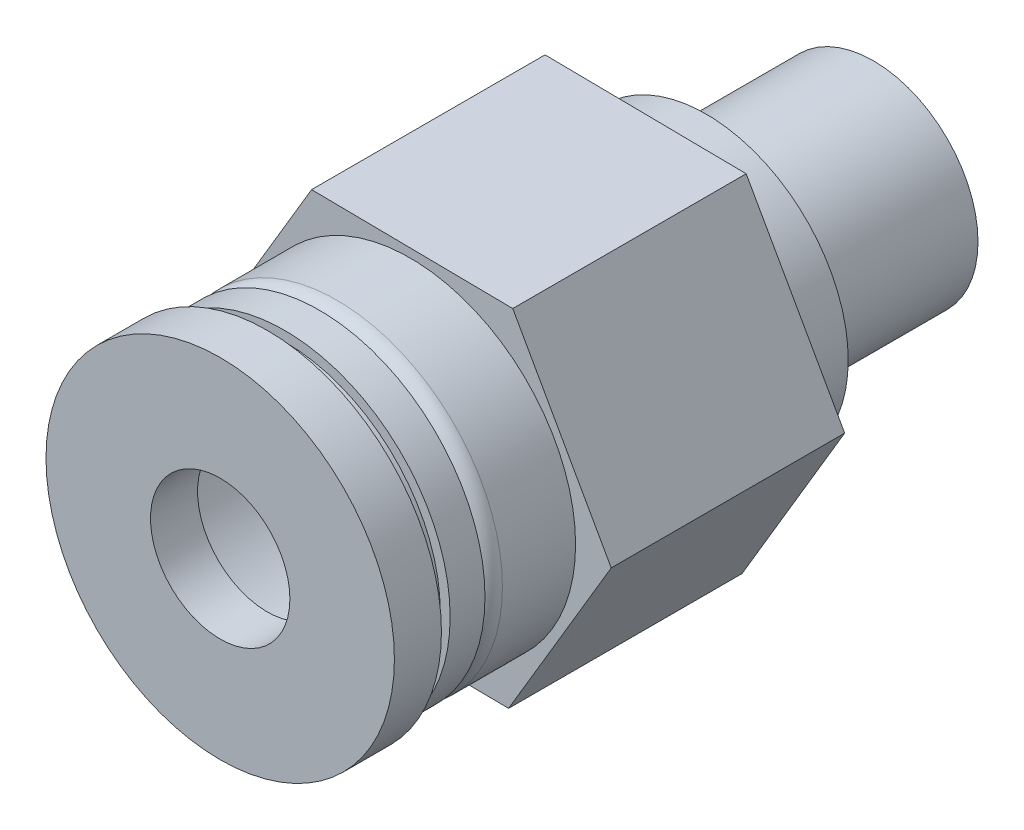
SolidWorks part; units mm, degrees
ref_plane "前视基准面" through (0, 0, 0) normal (0, 0, 1) x (1, 0, 0)
ref_plane "上视基准面" through (0, 0, 0) normal (0, 1, 0) x (1, 0, 0)
ref_plane "右视基准面" through (0, 0, 0) normal (1, 0, 0) x (0, 0, -1)
sketch "草图1" plane through (0, 0, 0) normal (0, 0, 1) x (1, 0, 0)
  circle A0 centre (0, 0) radius 3
  dimension "D1" = 6
extrude "凸台-拉伸1" add sketch "草图1" along normal blind 6.7
cosmetic thread "装饰螺纹线1" parameters "D1"=5.9, "D2"=4.917
sketch "草图2" plane through (0, 0, 6.7) normal (0, 0, 1) x (1, 0, 0)
  line L1 (2.8269, -5.0341) -> (5.7731, -0.0689)
  line L2 (5.7731, -0.0689) -> (2.9462, 4.9652)
  line L3 (2.9462, 4.9652) -> (-2.8269, 5.0341)
  line L4 (-2.8269, 5.0341) -> (-5.7731, 0.0689)
  line L5 (-5.7731, 0.0689) -> (-2.9462, -4.9652)
  line L6 (-2.9462, -4.9652) -> (2.8269, -5.0341)
  circle A0 centre (0, 0) radius 5 construction
  circle A1 centre (0, 0) radius 3
  dimension "D2" = 6
  dimension "D1" = 10
extrude "凸台-拉伸2" add sketch "草图2" along normal blind 6.7 separate body
sketch "草图3" plane through (0, 0, 0) normal (0, 0, -1) x (-1, 0, 0)
  circle A0 centre (0, 0) radius 3.2
extrude "切除-拉伸1" cut sketch "草图3" against normal blind 0.1
sketch "草图4" plane through (0, 0, 0.1) normal (0, 0, -1) x (-1, 0, 0)
  circle A0 centre (0, 0) radius 2.15
  dimension "D1" = 4.3
extrude "切除-拉伸2" cut sketch "草图4" against normal blind 12.6
sketch "草图5" plane through (0, 0, 13.4) normal (0, 0, 1) x (1, 0, 0)
  circle A0 centre (0, 0) radius 4.75
  circle A1 centre (0, 0) radius 3.75
  dimension "D1" = 7.5
  dimension "D2" = 9.5
extrude "凸台-拉伸3" add sketch "草图5" along normal blind 2.6
fillet "圆角1" radius 0.5 1 edges at (4.75, 0, 16)
sketch "草图6" plane through (0, 0, 16) normal (0, 0, 1) x (1, 0, 0)
  circle A0 centre (0, 0) radius 4.75
  circle A1 centre (0, 0) radius 3.75
  dimension "D1" = 7.5
  dimension "D2" = 9.5
extrude "凸台-拉伸4" add sketch "草图6" along normal blind 1
sketch "草图7" plane through (0, 0, 17) normal (0, 0, 1) x (1, 0, 0)
  circle A0 centre (0, 0) radius 4.4657
  circle A1 centre (0, 0) radius 4.177
extrude "凸台-拉伸5" add sketch "草图7" along normal blind 0.5 separate body
sketch "草图8" plane through (0, 0, 17.5) normal (0, 0, 1) x (1, 0, 0)
  circle A0 centre (0, 0) radius 5
  circle A1 centre (0, 0) radius 2
  dimension "D1" = 4
  dimension "D2" = 10
extrude "凸台-拉伸6" add sketch "草图8" along normal blind 1.35
sketch "草图9" plane through (0, 0, 6.7) normal (0, 0, -1) x (-1, 0, 0)
  circle A0 centre (0, 0) radius 4.075
  circle A1 centre (0, 0) radius 3
  circle A2 centre (0, 0) radius 3 construction
  dimension "D1" = 8.15
extrude "凸台-拉伸7" add sketch "草图9" along normal blind 1.8
